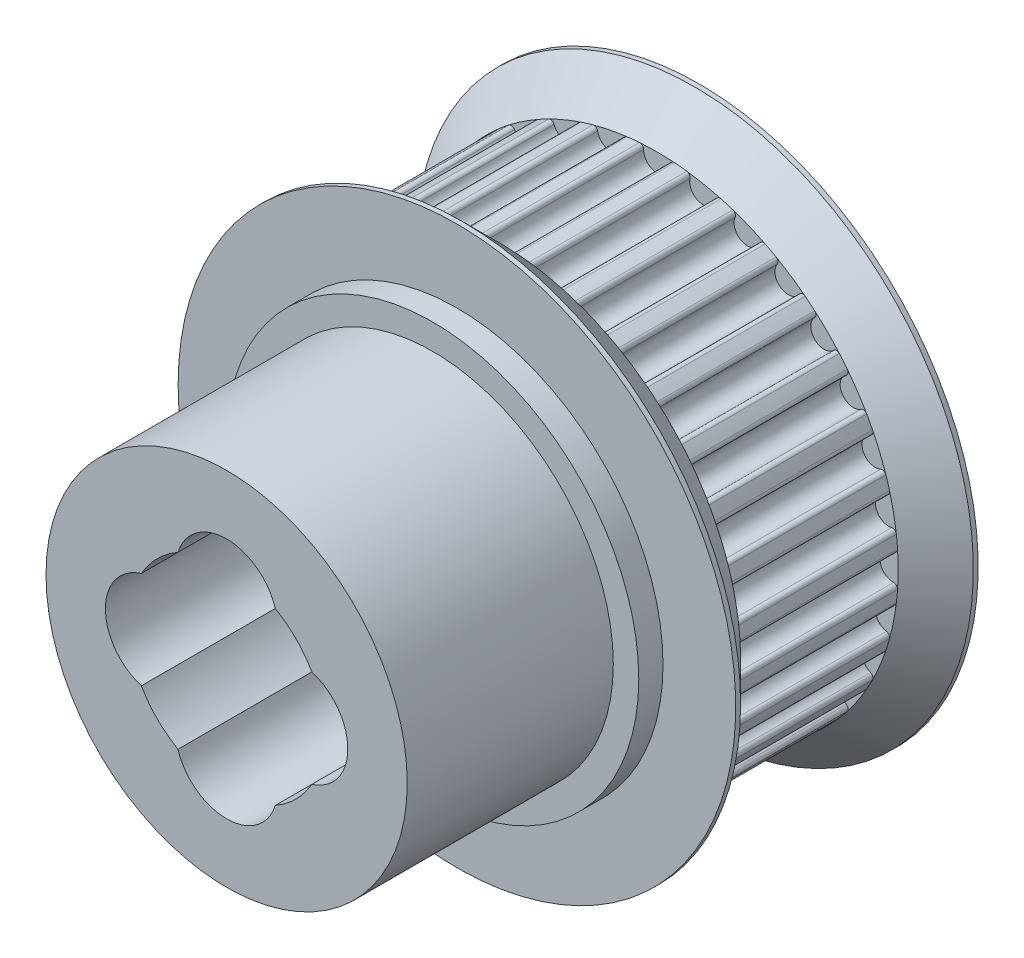
SolidWorks part; units mm, degrees
other "Camera1"
other "Camera2"
other "Camera3"
ref_plane "Front" through (0, 0, 0) normal (0, 0, 1) x (1, 0, 0)
ref_plane "Top" through (0, 0, 0) normal (0, 1, 0) x (1, 0, 0)
ref_plane "Right" through (0, 0, 0) normal (1, 0, 0) x (0, 0, -1)
sketch "Sketch1" plane through (0, 0, 0) normal (1, 0, 0) x (0, 0, -1)
  line L0 (0, 0) -> (-24.4032, 0) construction
  line L4 (-1.75, 9.95) -> (-8.25, 9.95)
  line L5 (-10, 11.5) -> (-10, 2.55)
  line L6 (-10, 2.55) -> (0, 2.55)
  line L7 (0, 2.55) -> (0, 11.5)
  line L9 (-0.2, 11.5) -> (-1.75, 9.95)
  line L11 (-5, 9.95) -> (-5, 22.0506) construction
  line L12 (-9.8, 11.5) -> (-8.25, 9.95)
  line L17 (-10, 11.5) -> (-9.8, 11.5)
  line L18 (-0.2, 11.5) -> (0, 11.5)
  dimension "D1" = 135
  dimension "D2" = 10
  dimension "D3" = 6.5
  dimension "D4" = 19.9
  dimension "D5" = 23
  dimension "D8" = 5.1
revolve "Revolve1" add sketch "Sketch1" angle 360 about L0
ref_plane "Plane2" through (0, 0, 1.75) normal (0, 0, 1) x (1, 0, 0)
ref_plane "Plane3" through (0, 0, 8.25) normal (0, 0, 1) x (1, 0, 0)
sketch "Sketch2" plane through (0, 0, 1.75) normal (0, 0, 1) x (1, 0, 0)
  circle A0 centre (0, 9.75) radius 0.55
  circle A2 centre (1.9021, 9.5627) radius 0.55
  circle A3 centre (3.7312, 9.0078) radius 0.55
  circle A4 centre (5.4168, 8.1068) radius 0.55
  circle A5 centre (6.8943, 6.8943) radius 0.55
  circle A6 centre (8.1068, 5.4168) radius 0.55
  circle A7 centre (9.0078, 3.7312) radius 0.55
  circle A8 centre (9.5627, 1.9021) radius 0.55
  circle A9 centre (9.75, 0) radius 0.55
  circle A10 centre (9.5627, -1.9021) radius 0.55
  circle A11 centre (9.0078, -3.7312) radius 0.55
  circle A12 centre (8.1068, -5.4168) radius 0.55
  circle A13 centre (6.8943, -6.8943) radius 0.55
  circle A14 centre (5.4168, -8.1068) radius 0.55
  circle A15 centre (3.7312, -9.0078) radius 0.55
  circle A16 centre (1.9021, -9.5627) radius 0.55
  circle A17 centre (0, -9.75) radius 0.55
  circle A18 centre (-1.9021, -9.5627) radius 0.55
  circle A19 centre (-3.7312, -9.0078) radius 0.55
  circle A20 centre (-5.4168, -8.1068) radius 0.55
  circle A21 centre (-6.8943, -6.8943) radius 0.55
  circle A22 centre (-8.1068, -5.4168) radius 0.55
  circle A23 centre (-9.0078, -3.7312) radius 0.55
  circle A24 centre (-9.5627, -1.9021) radius 0.55
  circle A25 centre (-9.75, 0) radius 0.55
  circle A26 centre (-9.5627, 1.9021) radius 0.55
  circle A27 centre (-9.0078, 3.7312) radius 0.55
  circle A28 centre (-8.1068, 5.4168) radius 0.55
  circle A29 centre (-6.8943, 6.8943) radius 0.55
  circle A30 centre (-5.4168, 8.1068) radius 0.55
  circle A31 centre (-3.7312, 9.0078) radius 0.55
  circle A32 centre (-1.9021, 9.5627) radius 0.55
  point P68 (0, 0)
  dimension "D1" = 1.1
  dimension "D2" = 9.75
  dimension "D3" = 32
extrude "Cut-Extrude1" cut sketch "Sketch2" along normal up to surface (6.5 mm away) up to plane "Plane3"
fillet "Fillet1" radius 0.16 64 edges at (-5.9506, 7.9745, 5) (-5.0902, 8.5494, 5) (-7.3921, 6.6603, 5) (-6.6603, 7.3921, 5) (-8.5494, 5.0902, 5) (-7.9745, 5.9506, 5) (-9.3782, 3.3245, 5) (-8.9822, 4.2806, 5) (-9.8466, 1.4311, 5) (-9.6447, 2.446, 5) (-9.9365, -0.5174, 5) (-9.9365, 0.5174, 5) (-9.6447, -2.446, 5) (-9.8466, -1.4311, 5) (-8.9822, -4.2806, 5) (-9.3782, -3.3245, 5) (-7.9745, -5.9506, 5) (-8.5494, -5.0902, 5) (-6.6603, -7.3921, 5) (-7.3921, -6.6603, 5) (-5.0902, -8.5494, 5) (-5.9506, -7.9745, 5) (-3.3245, -9.3782, 5) (-4.2806, -8.9822, 5) (-1.4311, -9.8466, 5) (-2.446, -9.6447, 5) (0.5174, -9.9365, 5) (-0.5174, -9.9365, 5) (2.446, -9.6447, 5) (1.4311, -9.8466, 5) (4.2806, -8.9822, 5) (3.3245, -9.3782, 5) (5.9506, -7.9745, 5) (5.0902, -8.5494, 5) (7.3921, -6.6603, 5) (6.6603, -7.3921, 5) (8.5494, -5.0902, 5) (7.9745, -5.9506, 5) (9.3782, -3.3245, 5) (8.9822, -4.2806, 5) (9.8466, -1.4311, 5) (9.6447, -2.446, 5) (9.9365, 0.5174, 5) (9.9365, -0.5174, 5) (9.6447, 2.446, 5) (9.8466, 1.4311, 5) (8.9822, 4.2806, 5) (9.3782, 3.3245, 5) (7.9745, 5.9506, 5) (8.5494, 5.0902, 5) (6.6603, 7.3921, 5) (7.3921, 6.6603, 5) (5.0902, 8.5494, 5) (5.9506, 7.9745, 5) (3.3245, 9.3782, 5) (4.2806, 8.9822, 5) (1.4311, 9.8466, 5) (2.446, 9.6447, 5) (-0.5174, 9.9365, 5) (0.5174, 9.9365, 5) (-2.446, 9.6447, 5) (-1.4311, 9.8466, 5) (-4.2806, 8.9822, 5) (-3.3245, 9.3782, 5)
sketch "Sketch3" plane through (0, 0, 10) normal (0, 0, 1) x (1, 0, 0)
  circle A0 centre (0, 0) radius 2.55
  circle A1 centre (0, 0) radius 7.5
  circle A2 centre (0, 0) radius 2.55 construction
  dimension "D1" = 15
sketch "草图1" plane through (0, 0, 10) normal (0, 0, 1) x (1, 0, 0)
  line L0 (0, 7.55) -> (0, -7.55) construction
  line L1 (7.55, 0) -> (-7.55, 0) construction
  circle A0 centre (0, 0) radius 7.45
  dimension "D1" = 14.9
extrude "凸台-拉伸1" add sketch "草图1" along normal blind 9.5
sketch "草图3" plane through (0, 0, 19.5) normal (0, 0, 1) x (1, 0, 0)
  line L0 (-5, 0) -> (5, 0) construction
  line L1 (0, 5) -> (0, -5) construction
  circle A0 centre (0, 0) radius 4.05
  circle A1 centre (0, 0) radius 5 construction
  arc A2 (3.5177, 2.0071) -> (3.5177, -2.0071) centre (2.9, 0) cw
  arc A3 (-2.0071, -3.5177) -> (2.0071, -3.5177) centre (0, -2.9) ccw
  arc A4 (-3.5177, 2.0071) -> (-3.5177, -2.0071) centre (-2.9, 0) ccw
  arc A5 (-2.0071, 3.5177) -> (2.0071, 3.5177) centre (0, 2.9) cw
  point P20 (0, 5)
  point P21 (5, 0)
  point P22 (0, -5)
  point P23 (-5, 0)
  dimension "D1" = 8.1
  dimension "D2" = 10
  dimension "D3" = 2.1
extrude "切除-拉伸2" cut sketch "草图3" against normal through all contours A0 | A5 A0 | A2 A0 | A0 A3 | A0 A4
sketch "草图4" plane through (0, 0, 10) normal (0, 0, 1) x (1, 0, 0)
  circle A0 centre (0, 0) radius 8.5
  circle A1 centre (0, 0) radius 7.45
  dimension "D1" = 17
extrude "凸台-拉伸2" add sketch "草图4" along normal blind 1
